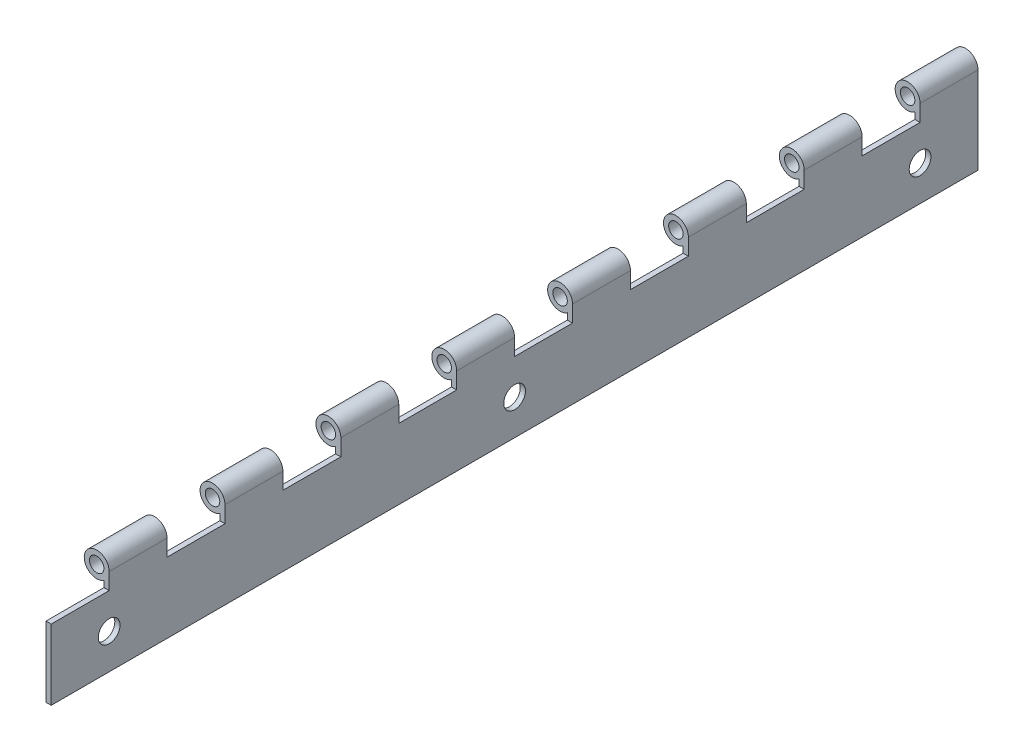
SolidWorks part; units mm, degrees
material "6061 Alloy"
ref_plane "Front Plane" through (0, 0, 0) normal (0, 0, 1) x (1, 0, 0)
ref_plane "Top Plane" through (0, 0, 0) normal (0, 1, 0) x (1, 0, 0)
ref_plane "Right Plane" through (0, 0, 0) normal (1, 0, 0) x (0, 0, -1)
sketch "Sketch1" plane through (0, 0, 0) normal (0, 0, 1) x (1, 0, 0)
  line L0 (5.461, 0) -> (5.461, -38.1)
  line L1 (5.461, -38.1) -> (3.175, -38.1)
  line L2 (3.175, -38.1) -> (3.175, -4.4432)
  circle A0 centre (0, 0) radius 3.175
  arc A1 (5.461, 0) -> (3.175, -4.4432) centre (0, 0) ccw
  circle A2 centre (0, 0) radius 5.461 construction
  dimension "D1" = 6.35
  dimension "D3" = 2.286
  dimension "D4" = 38.1
  dimension "D2" = 2.286
extrude "Boss-Extrude1" add sketch "Sketch1" along normal blind 406.4
sketch "Sketch2" plane through (5.461, 0, 0) normal (1, 0, 0) x (0, 0, -1)
  line L1 (-406.4, 5.461) -> (-381, 5.461)
  line L2 (-406.4, 5.461) -> (-406.4, -7.239)
  line L3 (-406.4, -7.239) -> (-381, -7.239)
  line L4 (-381, 5.461) -> (-381, -7.239)
  dimension "D1" = 12.7
  dimension "D2" = 25.4
extrude "Cut-Extrude1" cut sketch "Sketch2" against normal through all
pattern_linear "LPattern1" count 8 spacing 50.8 along (0, 0, -1) of "Cut-Extrude1"
sketch "Sketch3" plane through (3.175, 0, 0) normal (-1, 0, 0) x (0, 0, 1)
  line L0 (0, -4.4432) -> (0, -38.1) construction
  line L5 (25.4, -7.239) -> (25.4, -38.1) construction
  line L7 (406.4, -38.1) -> (0, -38.1) construction
  circle A0 centre (25.4, -22.6695) radius 4.7625
  circle A1 centre (203.2, -22.6695) radius 4.7625
  circle A2 centre (381, -22.6695) radius 4.7625
  dimension "D1" = 9.525
  dimension "D2" = 25.4
  dimension "D3" = 3
  dimension "D4" = 177.8
extrude "Cut-Extrude2" cut sketch "Sketch3" against normal through all
